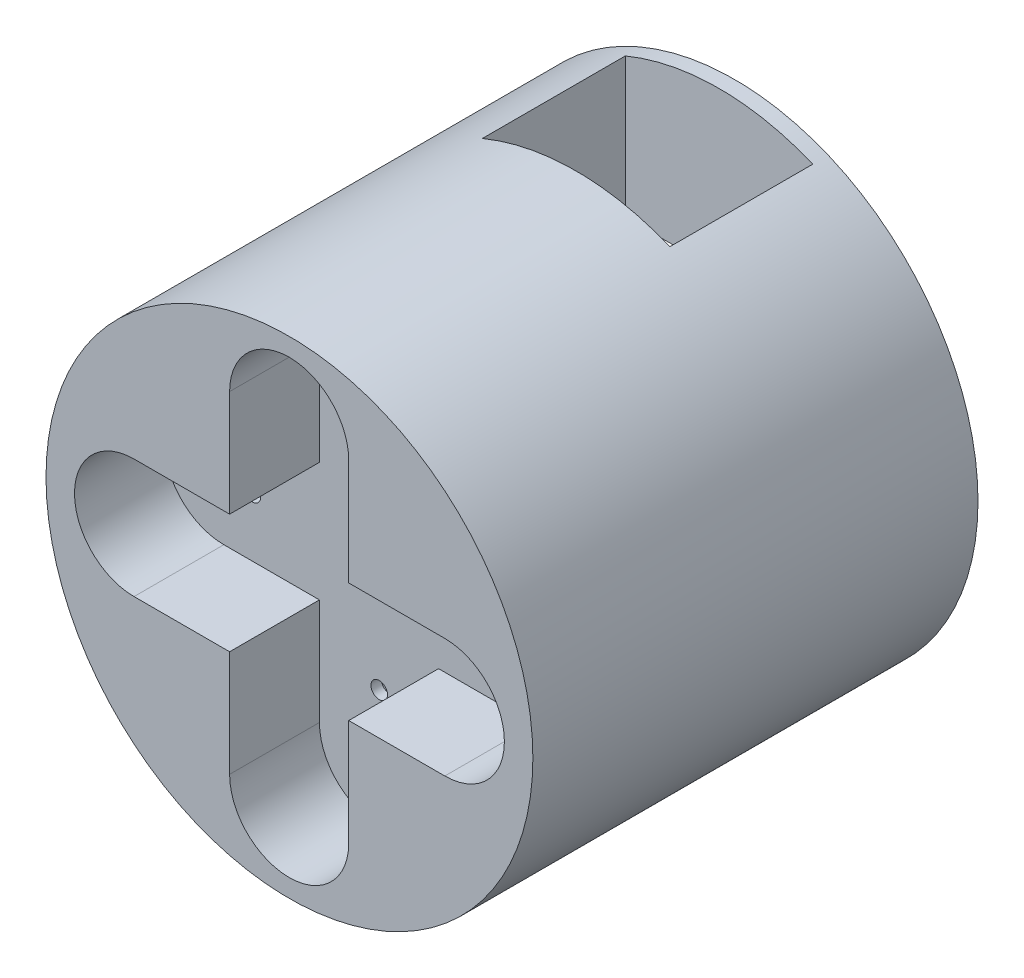
SolidWorks part; units mm, degrees
ref_plane "Front Plane" through (0, 0, 0) normal (0, 0, 1) x (1, 0, 0)
ref_plane "Top Plane" through (0, 0, 0) normal (0, 1, 0) x (1, 0, 0)
ref_plane "Right Plane" through (0, 0, 0) normal (1, 0, 0) x (0, 0, -1)
sketch "Sketch1" plane through (0, 0, 0) normal (0, 0, 1) x (1, 0, 0)
  circle A0 centre (0, 0) radius 23.5
  dimension "D1" = 47
extrude "Boss-Extrude1" add sketch "Sketch1" along normal blind 41.47 contours A0
sketch "Sketch5" plane through (0, 0, 0) normal (0, 0, -1) x (-1, 0, 0)
  line L1 (-9.05, 23.5) -> (9.05, 23.5)
  line L2 (-9.05, 23.5) -> (-9.05, -23.5)
  line L3 (-9.05, -23.5) -> (9.05, -23.5)
  line L4 (9.05, 23.5) -> (9.05, -23.5)
  dimension "D1" = 47
  dimension "D2" = 23.5
  dimension "D3" = 18.1
  dimension "D4" = 9.05
extrude "Cut-Extrude1" cut sketch "Sketch5" against normal blind 13.8
sketch "Sketch6" plane through (0, 0, 0) normal (0, 0, 1) x (1, 0, 0)
  circle A0 centre (0, 0) radius 23.5
  dimension "D1" = 47
extrude "Boss-Extrude2" add sketch "Sketch6" against normal blind 1.5
sketch "Sketch8" plane through (0, 0, -1.5) normal (0, 0, -1) x (-1, 0, 0)
  line L0 (-9.05, 8.2) -> (9.05, 8.2)
  line L2 (9.05, -21.6875) -> (9.05, 21.6875)
  line L3 (-9.05, 21.6875) -> (-9.05, -21.6875)
  line L4 (9.05, -21.6875) -> (9.05, 8.2)
  line L5 (-9.05, 8.2) -> (-9.05, -21.6875)
  arc A2 (9.05, 21.6875) -> (-9.05, 21.6875) centre (0, 0) ccw
  arc A3 (-9.05, -21.6875) -> (9.05, -21.6875) centre (0, 0) ccw
  arc A5 (-9.05, -21.6875) -> (9.05, -21.6875) centre (0, 0) ccw
  dimension "D2" = 8.2
  dimension "D1" = 0
extrude "Cut-Extrude5" cut sketch "Sketch8" against normal blind 1.5
sketch "Sketch9" plane through (0, 0, 41.47) normal (0, 0, 1) x (1, 0, 0)
  line L0 (-5.7752, 16) -> (-5.7752, 5.75)
  line L1 (5.7248, 16) -> (5.7248, 5.75)
  line L2 (-15, 5.75) -> (-5.7752, 5.75)
  line L3 (0, 0) -> (-0.019, 0)
  line L4 (-15, -5.75) -> (-5.7752, -5.75)
  line L5 (5.7248, -5.75) -> (5.7248, -16)
  line L6 (-5.7752, -5.75) -> (-5.7752, -16)
  line L7 (5.7248, -5.75) -> (15, -5.75)
  line L8 (5.7248, 5.75) -> (15, 5.75)
  arc A0 (5.7248, 16) -> (-5.7752, 16) centre (-0.0252, 16) ccw
  arc A1 (-15, 5.75) -> (-15, -5.75) centre (-15, 0) ccw
  arc A2 (15, -5.75) -> (15, 5.75) centre (15, 0) ccw
  arc A3 (-5.7752, -16) -> (5.7248, -16) centre (-0.0252, -16) ccw
  dimension "D1" = 32
  dimension "D2" = 30
  dimension "D3" = 16
  dimension "D4" = 15
extrude "Cut-Extrude10" cut sketch "Sketch9" against normal blind 8.67
sketch "Sketch13" plane through (0, 0, 32.8) normal (0, 0, 1) x (1, 0, 0)
  circle A0 centre (0, 0) radius 3
sketch "Sketch14" plane through (0, 0, 32.8) normal (0, 0, 1) x (1, 0, 0)
  circle A0 centre (0, 18.95) radius 0.8
  circle A1 centre (0, 18.95) radius 0.6681
  circle A2 centre (0, 10.4) radius 0.8
  circle A3 centre (0, 13.25) radius 0.8
  circle A4 centre (0, 16.1) radius 0.8
  circle A5 centre (0, -10.4) radius 0.8
  circle A6 centre (0, -13.25) radius 0.8
  circle A7 centre (0, -16.1) radius 0.8
  circle A8 centre (0, -18.95) radius 0.8
  circle A9 centre (12.25, 0) radius 0.8
  circle A10 centre (15.1, 0) radius 0.8
  circle A11 centre (17.95, 0) radius 0.8
  circle A12 centre (-12.25, 0) radius 0.8
  circle A13 centre (-15.1, 0) radius 0.8
  circle A14 centre (-17.95, 0) radius 0.8
  arc A15 (5.7248, 16) -> (-5.7752, 16) centre (-0.0252, 16) ccw construction
  arc A16 (-5.7752, -16) -> (5.7248, -16) centre (-0.0252, -16) ccw construction
  arc A17 (15, -5.75) -> (15, 5.75) centre (15, 0) ccw construction
  arc A18 (-15, 5.75) -> (-15, -5.75) centre (-15, 0) ccw construction
  arc A19 (-5.7752, -16) -> (5.7248, -16) centre (-0.0252, -16) ccw construction
  point P29 (-0.0252, 21.75)
  point P36 (-0.0252, -21.75)
  point P37 (20.75, 0)
  point P41 (-20.75, 0)
  point P45 (-0.0252, 21.75)
  point P46 (-0.0252, -21.75)
  dimension "D1" = 2.8
  dimension "D2" = 2.8
  dimension "D3" = 2.8
  dimension "D4" = 2.8
  dimension "D5" = 2.85
  dimension "D6" = 2.85
  dimension "D7" = 2.85
  dimension "D8" = 2.85
  dimension "D9" = 2.85
  dimension "D10" = 2.85
  dimension "D11" = 2.85
  dimension "D12" = 2.85
  dimension "D13" = 2.85
  dimension "D14" = 2.85
extrude "Cut-Extrude12" cut sketch "Sketch14" against normal blind 1
